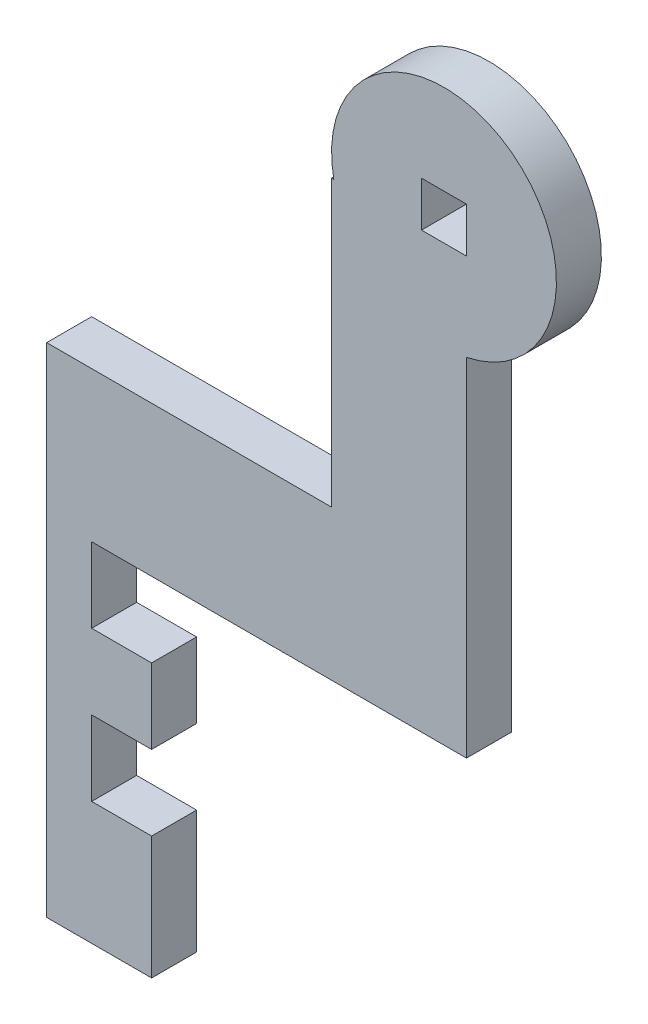
SolidWorks part; units mm, degrees
ref_plane "Front Plane" through (0, 0, 0) normal (0, 0, 1) x (1, 0, 0)
ref_plane "Top Plane" through (0, 0, 0) normal (0, 1, 0) x (1, 0, 0)
ref_plane "Right Plane" through (0, 0, 0) normal (1, 0, 0) x (0, 0, -1)
sketch "Sketch2" plane through (0, 0, 0) normal (0, 0, 1) x (1, 0, 0)
  line L1 (-14, 16.6) -> (14, 16.6)
  line L2 (-14, 16.6) -> (-14, -16.6)
  line L3 (-14, -16.6) -> (14, -16.6)
  line L4 (14, 16.6) -> (14, -16.6)
  line L5 (-14, 16.6) -> (14, -16.6) construction
  line L6 (-14, -16.6) -> (14, 16.6) construction
  point P0 (0, 0)
  dimension "D1" = 33.2
  dimension "D2" = 28
extrude "Boss-Extrude1" add sketch "Sketch2" along normal blind 3
sketch "Sketch4" plane through (0, 0, 3) normal (0, 0, 1) x (1, 0, 0)
  line L0 (14, -16.6) -> (14, 16.6) construction
  line L1 (14, 16.6) -> (-14, 16.6)
  line L2 (14, 16.6) -> (14, 6.6)
  line L3 (14, 6.6) -> (-14, 6.6)
  line L4 (-14, 16.6) -> (-14, 6.6)
  line L5 (14, 16.6) -> (-14, 16.6) construction
  line L6 (-14, -16.6) -> (14, -16.6) construction
  line L7 (14, 6.6) -> (-11, 6.6)
  line L8 (14, 6.6) -> (14, 1.6)
  line L9 (14, 1.6) -> (-11, 1.6)
  line L10 (-11, 6.6) -> (-11, 1.6)
  line L11 (14, 1.6) -> (-7, 1.6)
  line L12 (14, 1.6) -> (14, -3.4)
  line L13 (14, -3.4) -> (-7, -3.4)
  line L14 (-7, 1.6) -> (-7, -3.4)
  line L15 (14, -3.4) -> (-11, -3.4)
  line L16 (14, -3.4) -> (14, -8.4)
  line L17 (14, -8.4) -> (-11, -8.4)
  line L18 (-11, -3.4) -> (-11, -8.4)
  line L19 (14, -8.4) -> (-7, -8.4)
  line L20 (14, -8.4) -> (14, -16.6)
  line L21 (14, -16.6) -> (-7, -16.6)
  line L22 (-7, -8.4) -> (-7, -16.6)
  line M1 (14, -16.6) -> (14, 16.6)
  line M4 (-14, -16.6) -> (14, -16.6)
  dimension "D1" = 28
  dimension "D2" = 10
  dimension "D3" = 25
  dimension "D4" = 5
  dimension "D5" = 21
  dimension "D6" = 5
  dimension "D7" = 25
  dimension "D8" = 5
  dimension "D9" = 21
extrude "Cut-Extrude1" cut sketch "Sketch4" against normal blind 3 contours L3 L10 L9 M1 | L9 L14 L13 M1 | L15 L18 L17 L13 M1 | L17 L22 M4 M1
sketch "Sketch5" plane through (0, 0, 3) normal (0, 0, 1) x (1, 0, 0)
  line L0 (14, 35.6) -> (11, 38.6)
  line L1 (14, 16.6) -> (11, 16.6)
  line L2 (14, 16.6) -> (14, 35.6)
  line L3 (14, 35.6) -> (11, 35.6)
  line L4 (11, 16.6) -> (11, 35.6)
  line L5 (14, 35.6) -> (11, 35.6)
  line L6 (14, 35.6) -> (14, 38.6)
  line L7 (14, 38.6) -> (11, 38.6)
  line L8 (11, 35.6) -> (11, 38.6)
  line L9 (12.5, 37.1) -> (14, 38.6)
  line L10 (14, 16.6) -> (-14, 16.6) construction
  line L11 (11, 35.6) -> (5, 35.6)
  line L12 (11, 35.6) -> (11, 16.6)
  line L13 (11, 16.6) -> (5, 16.6)
  line L14 (5, 35.6) -> (5, 16.6)
  circle A0 centre (12.5, 37.1) radius 7.5
  line M3 (14, 16.6) -> (-14, 16.6)
  dimension "D4" = 15
  dimension "D1" = 19
  dimension "D2" = 3
  dimension "D3" = 3
  dimension "D5" = 6
extrude "Boss-Extrude2" add sketch "Sketch5" against normal blind 3 contours L11 A0 L12 | A0 L11 L14 L4 M3 | A0 L4 L2 M3 | L12 A0 L2 L3 | L2 A0 L11 L8 L7 L6
